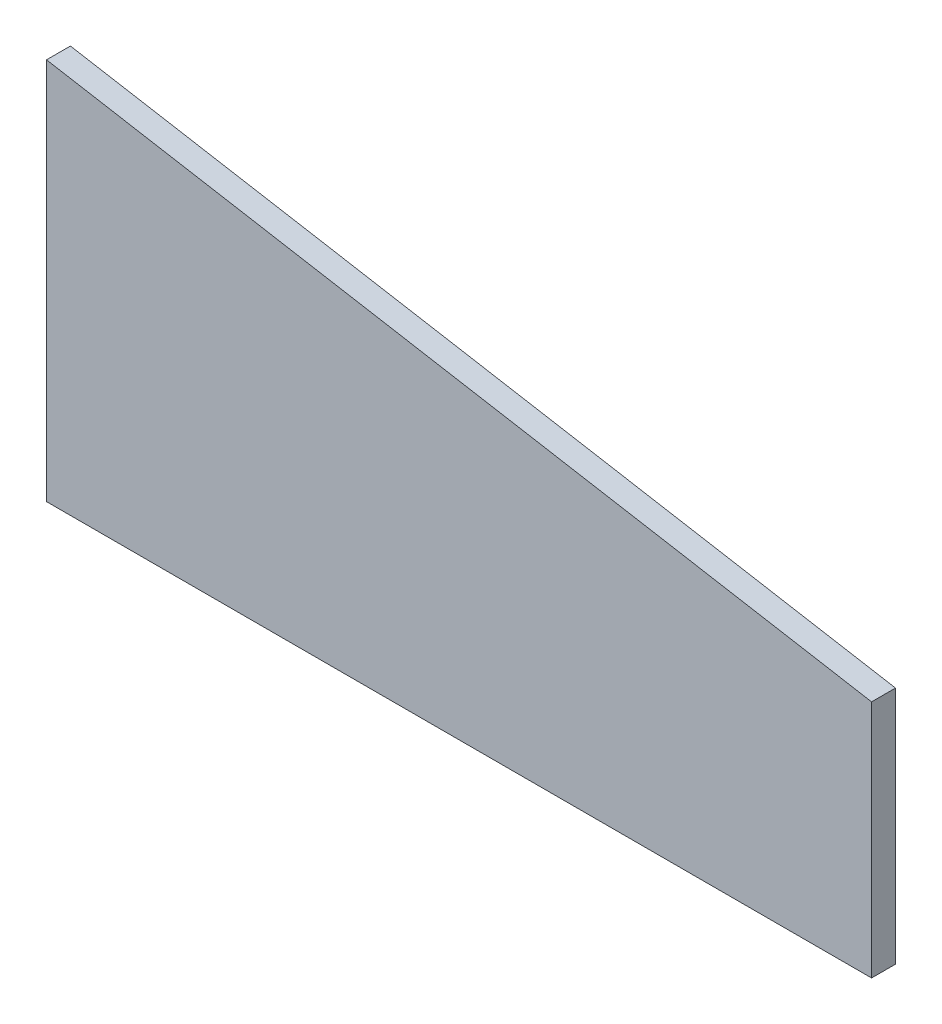
SolidWorks part; units mm, degrees
ref_plane "Front Plane" through (0, 0, 0) normal (0, 0, 1) x (1, 0, 0)
ref_plane "Top Plane" through (0, 0, 0) normal (0, 1, 0) x (1, 0, 0)
ref_plane "Right Plane" through (0, 0, 0) normal (1, 0, 0) x (0, 0, -1)
sketch "Sketch1" plane through (0, 0, 0) normal (0, 0, 1) x (1, 0, 0)
  line L0 (0, 0) -> (0, 101.6)
  line L1 (0, 101.6) -> (219.075, 63.5)
  line L2 (219.075, 63.5) -> (219.075, 0)
  line L3 (219.075, 0) -> (0, 0)
  dimension "D1" = 101.6
  dimension "D2" = 63.5
  dimension "D3" = 219.075
extrude "Boss-Extrude1" add sketch "Sketch1" along normal blind 6.35
